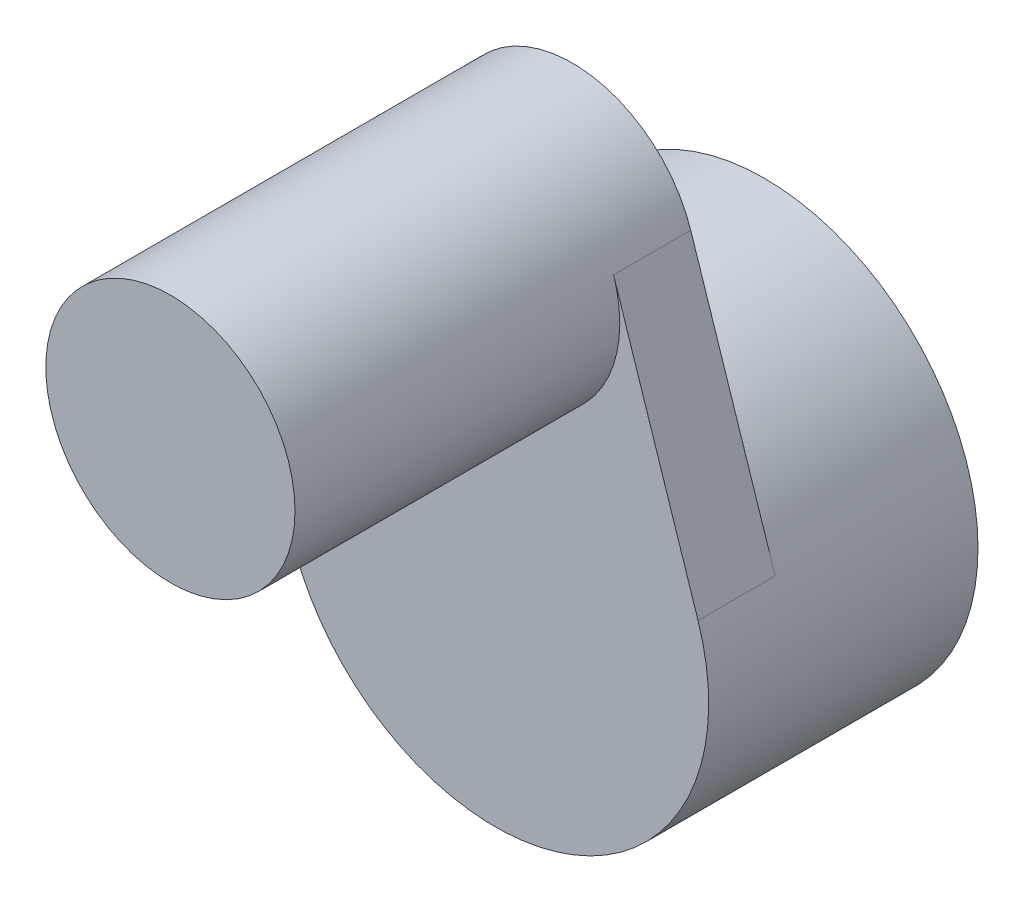
SolidWorks part; units mm, degrees
ref_plane "Front Plane" through (0, 0, 0) normal (0, 0, 1) x (1, 0, 0)
ref_plane "Top Plane" through (0, 0, 0) normal (0, 1, 0) x (1, 0, 0)
ref_plane "Right Plane" through (0, 0, 0) normal (1, 0, 0) x (0, 0, -1)
sketch "Sketch1" plane through (0, 0, 0) normal (0, 0, 1) x (1, 0, 0)
  circle A0 centre (0, 0) radius 2.3343
  circle A1 centre (0, 0) radius 3.3731
  dimension "D1" = 4.6685
  dimension "D2" = 6.7462
extrude "Boss-Extrude1" add sketch "Sketch1" along normal blind 4.2545
sketch "Sketch2" plane through (0, 0, 4.2545) normal (0, 0, 1) x (1, 0, 0)
  line L0 (-1.8701, 5.1144) -> (-3.2046, 1.0529)
  line L1 (0, 4.5) -> (0, 0) construction
  line L2 (1.8701, 5.1144) -> (3.2046, 1.0529)
  arc A0 (1.8701, 5.1144) -> (-1.8701, 5.1144) centre (0, 4.5) ccw
  circle A1 centre (0, 0) radius 3.3731 construction
  circle A2 centre (0, 4.5) radius 0.4699
  dimension "D1" = 3.937
  dimension "D2" = 0.9398
  dimension "D3" = 4.5
extrude "Boss-Extrude2" add sketch "Sketch2" against normal blind 1.2192
sketch "Sketch3" plane through (0, 0, 4.2545) normal (0, 0, 1) x (1, 0, 0)
  circle A0 centre (0, 0) radius 2.3343 construction
  circle A1 centre (0, 0) radius 2.3343
extrude "Boss-Extrude3" add sketch "Sketch3" against normal offset from surface (1.5621 mm away) 2.6924 up to face at (3.3731, 0, 0)
sketch "Sketch4" plane through (0, 0, 4.2545) normal (0, 0, 1) x (1, 0, 0)
  circle A0 centre (0, 4.5) radius 1.9685
  arc A1 (1.8701, 5.1144) -> (-1.8701, 5.1144) centre (0, 4.5) ccw construction
extrude "Boss-Extrude5" add sketch "Sketch4" along normal offset from surface (5.1308 mm away) 6.35 up to face at (0, 4.0022, 3.0353)
